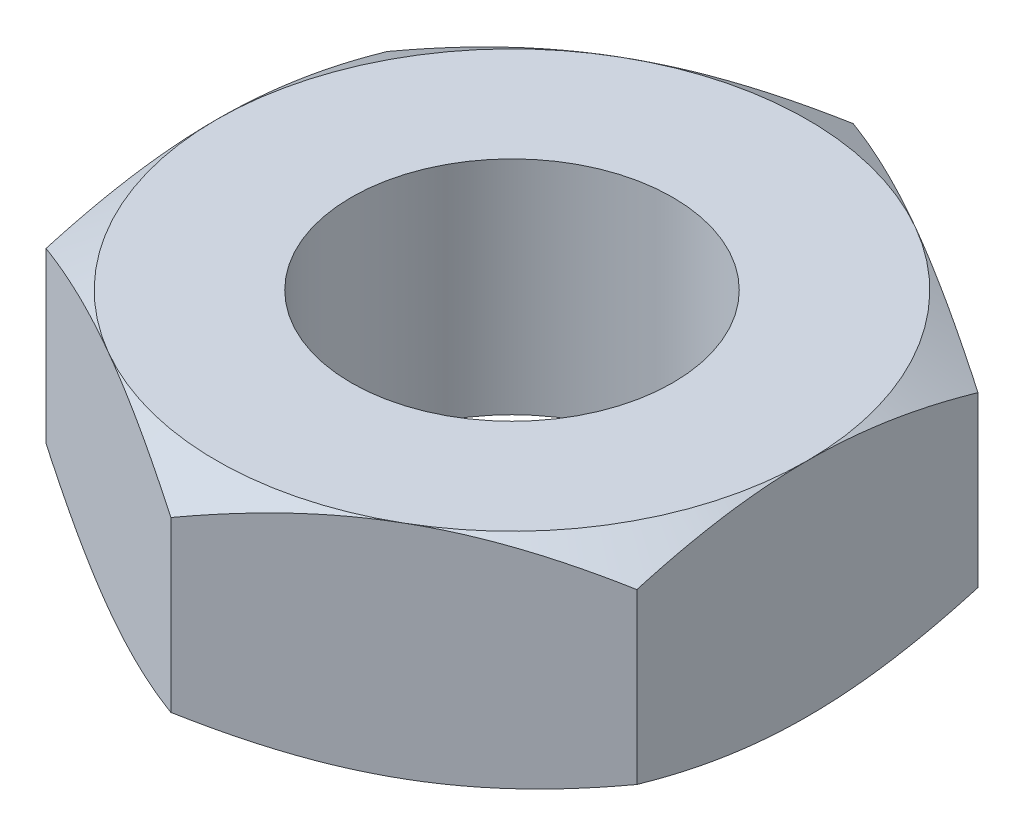
SolidWorks part; units mm, degrees
material "AISI 4130 Steel, normalized at 870C"
ref_plane "Front Plane" through (0, 0, 0) normal (0, 0, 1) x (1, 0, 0)
ref_plane "Top Plane" through (0, 0, 0) normal (0, 1, 0) x (1, 0, 0)
ref_plane "Right Plane" through (0, 0, 0) normal (1, 0, 0) x (0, 0, -1)
sketch "Sketch1" plane through (0, 0, 0) normal (0, 1, 0) x (1, 0, 0)
  line L1 (-6.35, 3.6662) -> (-6.35, -3.6662)
  line L2 (-6.35, -3.6662) -> (0, -7.3323)
  line L3 (0, -7.3323) -> (6.35, -3.6662)
  line L4 (6.35, -3.6662) -> (6.35, 3.6662)
  line L5 (6.35, 3.6662) -> (0, 7.3323)
  line L6 (0, 7.3323) -> (-6.35, 3.6662)
  circle A0 centre (0, 0) radius 6.35 construction
  dimension "Hex" = 12.7
extrude "Boss-Extrude1" add sketch "Sketch1" along normal mid plane 4.7625
hole_wizard "5/16-24 Tapped Hole1" positions "Sketch6" profile "Sketch7" tap size "5/16-24" standard "ANSI Inch" end condition through all
sketch "Sketch6" plane through (0, 2.3813, 0) normal (0, 1, 0) x (1, 0, 0)
  point P0 (0, 0)
sketch "Sketch7" plane through (0, 2.3813, 0) normal (1, 0, 0) x (0, 0, 1)
  line L0 (0, 0) -> (0, 4.7625)
  line L1 (0, 4.7625) -> (3.4544, 4.7625)
  line L2 (3.4544, 4.7625) -> (3.4544, 0)
  line L5 (3.4544, 0) -> (0, 0)
  line L11 (0, -6.35) -> (0, 107.95) construction
  dimension "Thru Tap Drill Dia." = 6.9088
  dimension "Thru Tap Drill Depth" = 4.7625
cosmetic thread "Hole Thread1" parameters "D2"=7.9375
sketch "Sketch5" plane through (0, 2.3813, 0) normal (0, 1, 0) x (1, 0, 0)
  circle A0 centre (0, 0) radius 6.35 construction
  circle A1 centre (0, 0) radius 6.35
extrude "Cut-Extrude2" cut sketch "Sketch5" against normal through all draft 60 flip side to cut
mirror "Mirror1" about plane through (0, 0, 0) normal (0, 1, 0) of "Cut-Extrude2"
move or copy body "Body-Move/Copy1" [suppressed] bodies to move or copy 107
move or copy body "Body-Move/Copy2" [suppressed] bodies to move or copy 107
move or copy body "Body-Move/Copy3" [suppressed] bodies to move or copy 107
move or copy body "Body-Move/Copy4" [suppressed] bodies to move or copy 107
